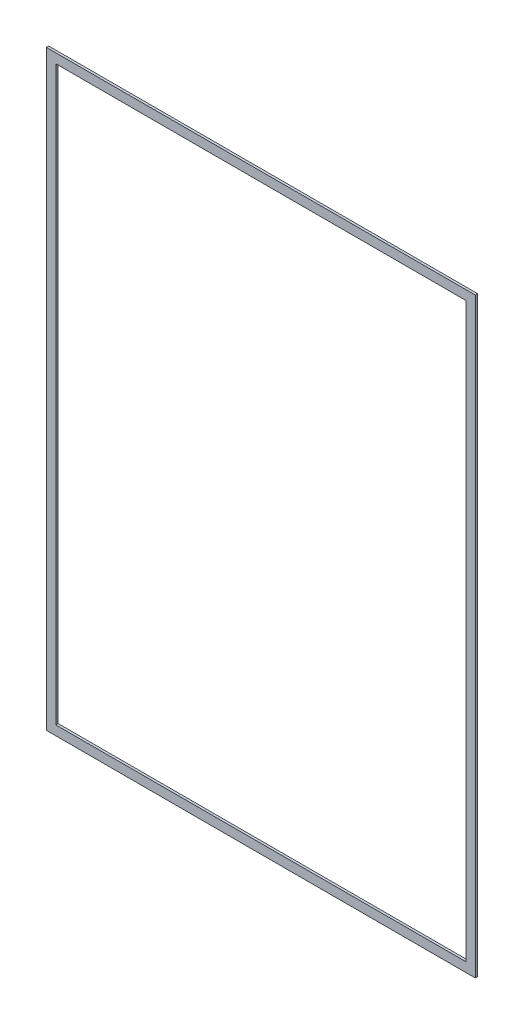
SolidWorks part; units mm, degrees
ref_plane "Front Plane" through (0, 0, 0) normal (0, 0, 1) x (1, 0, 0)
ref_plane "Top Plane" through (0, 0, 0) normal (0, 1, 0) x (1, 0, 0)
ref_plane "Right Plane" through (0, 0, 0) normal (1, 0, 0) x (0, 0, -1)
sketch "Sketch1" plane through (0, 0, 0) normal (0, 0, 1) x (1, 0, 0)
  line L0 (-276.3266, 385.8133) -> (276.3266, 385.8133)
  line L1 (-289.0266, -398.5133) -> (289.0266, -398.5133)
  line L2 (-289.0266, -398.5133) -> (-289.0266, 398.5133)
  line L3 (-289.0266, 398.5133) -> (289.0266, 398.5133)
  line L4 (289.0266, -398.5133) -> (289.0266, 398.5133)
  line L5 (-289.0266, -398.5133) -> (289.0266, 398.5133) construction
  line L6 (-289.0266, 398.5133) -> (289.0266, -398.5133) construction
  line L7 (276.3266, -385.8133) -> (276.3266, 385.8133)
  line L8 (-276.3266, -385.8133) -> (276.3266, -385.8133)
  line L9 (-276.3266, -385.8133) -> (-276.3266, 385.8133)
  point P0 (0, 0)
  dimension "D1" = 797.0266
  dimension "D2" = 578.0532
  dimension "D3" = 12.7
extrude "Boss-Extrude1" add sketch "Sketch1" along normal blind 3.175
equation "\"Height\"= 32in"
equation "\"Width\"= 23in"
equation "\"Depth\"= 20in"
equation "\"Plexi\"= .121in"
equation "\"EBWidth\" = 9in"
equation "\"ComponentMountDia\"=0.1770"
equation "\"MagnetThickness\"= .125in"
equation "\"MagnetDiameter\"= 12mm"
equation "\"DoorPlexi\" = \"Plexi\""
equation "\"ShelfThickness\" = .1250in"
equation "\"BasePlateThickness\" = 0.5in"
equation "\"BasePlateWidth\" = \"Width\"+\"EBWidth\"-2*\"Plexi\""
equation "\"BasePlateDepth\" = \"TopBarDepth\"+2*\"CornerCube\""
equation "\"Boxsize\" = .75in"
equation "\"BoxsizeHalf\" = \"Boxsize\"/2"
equation "\"Boxinner\" = .625in"
equation "\"CornerCube\" = 0.75in"
equation "\"FingerLength\" = 1.125in"
equation "\"FingerWidth\" = .625in"
equation "\"Cutwidth\"= .016in"
equation "\"Earsize\"= 1in + \"Cutwidth\" /2"
equation "\"Slotsize\" = 1in - \"CutWidth\" / 2"
equation "\"InnerWidth\" = \"Width\" - 2* \"Plexi\""
equation "\"InnerHeight\" = \"Height\" -2 * \"Plexi\""
equation "\"InnerDepth\" = \"Depth\" - 2*\"Plexi\""
equation "\"FrontDoorGap\" = .1in"
equation "\"TopDepth\" = \"Depth\"-\"DoorPlexi\"-\"FrontDoorGap\""
equation "\"TopBarDepth\" = \"Depth\"-\"DoorPlexi\"-\"Plexi\"-2*\"MagnetThickness\"-2*\"CornerCube\""
equation "\"RearNumHoles\" = 4"
equation "\"RearHolesBorder\" = 2.25"
equation "\"RearHoleSpacing\" = (\"Width\" - 2*\"RearHolesBorder\") / (\"RearNumHoles\"-1)"
equation "\"RearBarLength\" = (\"InnerWidth\"-2*\"CornerCube\")"
equation "\"RearTopNumHoles\" = 4"
equation "\"RearTopHolesBorder\" = 3.1"
equation "\"RearTopHolesSpacing\" = (\"Width\" - 2*\"RearTopHolesBorder\") / (\"RearTopNumHoles\"-1)"
equation "\"SideTopNumHoles\" = 4"
equation "\"SideTopHoleOffset\"=\"CornerCube\"+\"FingerLength\"+\"Plexi\"+.5"
equation "\"SideTopHoleSpacing\" = (\"TopBarDepth\"-2*\"SideTopHoleOffset\") / (\"SideTopNumHoles\"-1)"
equation "\"SideHorizNumHoles\" = 4"
equation "\"SideHorizHoleBorder\" = 1.50"
equation "\"SideHorizHoleSpacing\" = (\"TopBarDepth\"-2*\"SideHorizHoleBorder\") / (\"SideHorizNumHoles\"-1)"
equation "\"SideVertBarLength\"=\"Height\"-\"BasePlateThickness\"-2*\"CornerCube\"-\"Plexi\""
equation "\"SideVertNumHoles\" = 4"
equation "\"SideVertHolesBorder\" = \"CornerCube\"+\"FingerLength\"+1.50"
equation "\"SideVertHoleSpacing\" = (\"InnerHeight\" - 2*\"SideVertHolesBorder\") / (\"SideVertNumHoles\"-1)"
equation "\"RearSideVertNumHoles\" = 4"
equation "\"RearSideVertHolesBorder\" = 2.4"
equation "\"RearSideVertHoleSpacing\" = (\"InnerHeight\" - 2*\"RearSideVertHolesBorder\") / (\"RearSideVertNumHoles\"-1)"
equation "\"Rivet3_16Dia\" = .191in"
equation "\"RivetDia\" = .228in"
equation "\"BinderPostDia\" = .228in"
equation "\"SlotDepth\" = \"Plexi\" + 0.75in + .005in"
equation "\"SideSlotWidth\"   = \"Plexi\"+.005in"
equation "\"SidePanelVertSpacing\" = (\"Height\"-2*(1.75-\"Plexi\")) / 5"
equation "\"BottomPanelSideHoleSpacing\" = (\"InnerDepth\"-2*(1.75-\"Plexi\")) / 4"
equation "\"CoolerDepth\" = 12in"
equation "\"ShelfGap\" = 0.5in"
equation "\"ShelfDepth\" = \"TopBarDepth\"+\"CornerCube\"-\"CoolerDepth\""
equation "\"ShelfBarDepth\"=\"ShelfDepth\"-2*\"CornerCube\""
equation "\"ShelfWidth\" = \"EBWidth\"-\"ShelfGap\""
equation "\"ShelfBarWidth\" = \"EBWidth\"-\"Boxsize\""
equation "\"ShelfBarWidthShort\" = \"ShelfBarWidth\"-\"Boxsize\"-\"ShelfGap\""
equation "\"ShelfHeight1\" = 13in"
equation "\"ShelfHeight2\" = 24in"
equation "\"IntakeWidth\"=4in"
equation "\"IntakeHeight\"=2in"
equation "\"ExhaustWidth\"=4in"
equation "\"ExhaustHeight\"=2in"
equation "\"VentSpacing\"=7in"
equation "\"VentVertLocation\"=12.75in"
equation "\"AngleBracketLengthShort\"=.625in"
equation "\"AngleBracketLengthLong\"=1in"
equation "\"AngleBracketWidth\"=.5in"
equation "\"AngleBracketThickness\"=.125in"
equation "\"AngleBracketHolePosShort\"=.3125in"
equation "\"AngleBracketHolePosLong\"=.640625in"
equation "\"AngleBracketHoleDia\"=\"Rivet3_16Dia\""
equation "\"ShelfBarAngleHole\"=\"ShelfGap\"+\"Boxsize\"+\"AngleBracketHolePosShort\""
equation "\"PSBracketThickness\" = .0641in"
equation "\"EBForwardMountOffset\" = 4.0in"
equation "\"EBForwardMount\" = 2*\"Boxsize\"+\"CoolerDepth\"+\"EBForwardMountOffset\""
equation "\"EBRearwardMountOffset\" = 1.5in"
equation "\"EBRearwardMount\"= \"Boxsize\"+\"EBRearwardMountOffset\""
equation "\"MagSealWidth\" = \"InnerWidth\""
equation "\"MagSealHeight\" = \"Height\"-\"BasePlateThickness\"-\"Plexi\""
equation "\"MagWidth\" = .500in"
equation "\"D1@Sketch1\"=\"MagSealHeight\""
equation "\"D2@Sketch1\"=\"MagSealWidth\""
equation "\"D3@Sketch1\"=\"MagWidth\""
equation "\"D1@Boss-Extrude1\"=\"MagnetThickness\""
